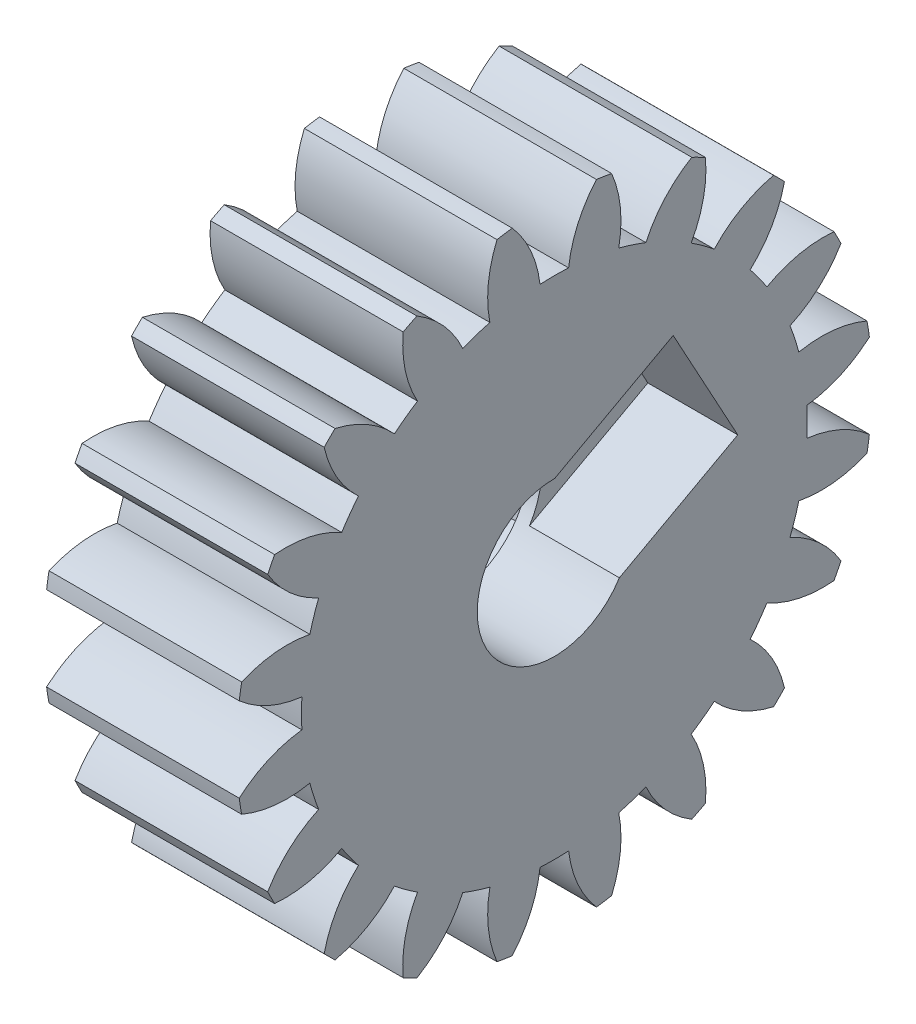
SolidWorks part; units mm, degrees
ref_plane "Plane1" through (0, 0, 0) normal (0, 0, 1) x (1, 0, 0)
ref_plane "Plane2" through (0, 0, 0) normal (0, 1, 0) x (1, 0, 0)
ref_plane "Plane3" through (0, 0, 0) normal (1, 0, 0) x (0, 0, -1)
sketch "HoldingSke" plane through (0, 0, 0) normal (0, 1, 0) x (1, 0, 0)
  line L0 (0, 0) -> (0.4176, -0.152)
  line L1 (-15, 0) -> (100, 0) construction
  line L2 (0, 0) -> (-2.1039, 2.3779)
  line L3 (0, 0) -> (-11.863, 4.5341)
  line L4 (0, 0) -> (8.1152, 2.9537)
  line L5 (0, 0) -> (-46.8476, -17.4728)
  line L6 (0, 0) -> (-8.2896, -5.593)
  line L7 (-2.1039, 2.3779) -> (8.6586, 51.2059)
  line L8 (-76.2, 54.61) -> (-76.1, 54.61)
  line L9 (-71.009, 38.7566) -> (-53.1078, 45.2721)
  line L10 (-76.2, 71.12) -> (104.1128, 71.12)
  line L11 (0, 0) -> (-10, 0)
  line L12 (-76.2, 101.6) -> (-76.123, 101.6)
  line L13 (24.9733, 27.94) -> (52.9518, 28.4284)
  line L14 (24.9733, 27.94) -> (24.9743, 27.94)
  line L15 (24.9733, 27.94) -> (100.4006, 29.5858)
  line L16 (-63.627, -2.25) -> (-12.827, -2.25)
  circle A0 centre (0, 0) radius 0.4
  circle A1 centre (0, 0) radius 19.6865
  circle A2 centre (0, 0) radius 37.5
  circle A3 centre (0, 0) radius 0.4
  dimension "MHD" = 39.373
  dimension "Hub_dia" = 75
  dimension "Bore" = 0.8
  dimension "MBD" = 0.8
  dimension "Num_teeth" = 20
  dimension "Pitch_radius" = 180.3128
  dimension "Pitch" = 0.4444
  dimension "Width" = 10
  dimension "Overall_len" = 50
  dimension "Show_teeth" = 20
  dimension "Thickness" = 10
  dimension "OAL" = 50.0001
  dimension "T_dim" = 0.1
  dimension "Ap" = 20
  dimension "H" = 19.05
  dimension "Backlash" = 0.077
  dimension "Addendum_fac" = 1
  dimension "Dedendum_fac" = 1.25
  dimension "Clearance_fac" = 0.25
  dimension "Dedendum_add" = 0.001
  dimension "Module" = 2.25
sketch "BasProSke" plane through (0, 0, 0) normal (0, 1, 0) x (1, 0, 0)
  line L0 (-10, 0) -> (60, 0) construction
  line L1 (0, 0) -> (0, 24.75)
  line L2 (0, 0) -> (15, 0)
  line L3 (15, 0) -> (15, 24.75)
  line L4 (15, 24.75) -> (0, 24.75)
  dimension "Diameter" = 49.5
  dimension "Thickness" = 15
revolve "Base-Revolve" add sketch "BasProSke" angle 360 about L0
sketch "TooCutSke" plane through (0, 0, 0) normal (1, 0, 0) x (0, 0, -1)
  line L1 (0, 0) -> (0, 107) construction
  line L2 (0, 0) -> (-1.9, 22.4196) construction
  line L3 (0, 0) -> (-7.021, 44.3291) construction
  line L4 (-1.9, 22.4196) -> (-3.5105, 22.1646) construction
  arc A0 (1.1119, 19.6551) -> (-1.1119, 19.6551) centre (0, 0) ccw
  arc A1 (3.3, 24.5546) -> (-3.3, 24.5546) centre (0, 0) ccw
  circle A2 centre (0, 0) radius 22.5 construction
  circle A3 centre (0, 0) radius 21.1431 construction
  arc A4 (-1.1119, 19.6551) -> (-3.3, 24.5546) centre (-10.0501, 18.6018) ccw
  arc A5 (3.3, 24.5546) -> (1.1119, 19.6551) centre (10.0501, 18.6018) ccw
  dimension "Root_dia" = 39.373
  dimension "Overcut_dia" = 49.5508
  dimension "Pitch_dia" = 45
  dimension "Base_dia" = 42.2862
  dimension "Flank_rad" = 9
  dimension "Half_ang" = 9
  dimension "Half_CT" = 1.6306
extrude "ToothCut" cut sketch "TooCutSke" along normal through all
fillet "Breaks" [suppressed] radius 0.045
fillet "RootFillets" [suppressed] radius 0.5635
pattern_circular "TeethCuts" count 20 over 360 about axis through (0, 0, 0) along (1, 0, 0) of "ToothCut", "RootFillets", "Breaks"
sketch "HubNeaOneSke" plane through (0, 0, 0) normal (-1, 0, 0) x (0, 0, 1)
  circle A0 centre (0, 0) radius 19.6865
  dimension "Diameter" = 39.373
extrude "HubNearOne" [suppressed] add sketch "HubNeaOneSke" along normal blind 35.0001
sketch "HubNeaBotSke" plane through (0, 0, 0) normal (-1, 0, 0) x (0, 0, 1)
  circle A0 centre (0, 0) radius 19.6865
  dimension "Diameter" = 39.373
extrude "HubNearBoth" [suppressed] add sketch "HubNeaBotSke" along normal blind 17.5
ref_plane "FarPln" through (15, 0, 0) normal (1, 0, 0) x (0, 0, -1)
sketch "HubFarSke" plane through (15, 0, 0) normal (1, 0, 0) x (0, 0, -1)
  circle A0 centre (0, 0) radius 19.6865
  dimension "Diameter" = 39.373
extrude "HubFar" [suppressed] add sketch "HubFarSke" along normal blind 17.5
sketch "BorSke" plane through (0, 0, 0) normal (1, 0, 0) x (0, 0, -1)
  circle A0 centre (0, 0) radius 6
  dimension "Diameter" = 12
extrude "Bore" cut sketch "BorSke" along normal mid plane 100.0001
sketch "KeySke" plane through (0, 0, 0) normal (1, 0, 0) x (0, 0, -1)
  line L0 (-0.05, 0) -> (-0.05, 0.5)
  line L1 (-0.05, 0.5) -> (0.05, 0.5)
  line L2 (0.05, 0.5) -> (0.05, 0)
  line L3 (0, 0) -> (0, 34) construction
  line L4 (-0.05, 0) -> (0.05, 0)
  dimension "Offset" = 0.5
  dimension "Width" = 0.1
extrude "Keyway" [suppressed] cut sketch "KeySke" along normal mid plane 100.0001
pattern_circular "Keyway2" [suppressed] count 2 every 90 about axis through (-10, 0, 0) along (1, 0, 0)
sketch "Sketch1" plane through (15, 0, 0) normal (1, 0, 0) x (0, 0, -1)
  line L0 (0.0359, 5.9999) -> (5.0641, -3.2178)
  line L1 (0.0359, 5.9999) -> (9.2536, 11.0282)
  line L2 (5.0641, -3.2178) -> (14.2819, 1.8104)
  line L3 (9.2536, 11.0282) -> (14.2819, 1.8104)
  circle A0 centre (0, 0) radius 6
  circle A1 centre (0, 0) radius 6 construction
  dimension "D1" = 0
  dimension "D4" = 12
  dimension "D2" = 6
  dimension "D3" = 6
  dimension "D5" = 10.5
  dimension "D6" = 10.5
extrude "Cut-Extrude1" cut sketch "Sketch1" against normal blind 7 contours L0 A0 | L0 A0 | A0 L0 L2 L3 L1
sketch "Sketch2" plane through (0, 0, 0) normal (-1, 0, 0) x (0, 0, 1)
  line L1 (13.038, -4.6914) -> (10.5819, 8.9455)
  line L2 (10.5819, 8.9455) -> (-2.4561, 13.637)
  line L3 (-2.4561, 13.637) -> (-13.038, 4.6914)
  line L4 (-13.038, 4.6914) -> (-10.5819, -8.9455)
  line L5 (-10.5819, -8.9455) -> (2.4561, -13.637)
  line L6 (2.4561, -13.637) -> (13.038, -4.6914)
  line L7 (4.6914, 13.038) -> (-8.9455, 10.5819)
  line L8 (-8.9455, 10.5819) -> (-13.637, -2.4561)
  line L9 (-13.637, -2.4561) -> (-4.6914, -13.038)
  line L10 (-4.6914, -13.038) -> (8.9455, -10.5819)
  line L11 (8.9455, -10.5819) -> (13.637, 2.4561)
  line L12 (13.637, 2.4561) -> (4.6914, 13.038)
  circle A0 centre (0, 0) radius 12 construction
  circle A1 centre (0, 0) radius 6 construction
  circle A2 centre (0, 0) radius 12 construction
  dimension "D1" = 0
  dimension "D2" = 24
  dimension "D3" = 24
  dimension "D5" = 0
  dimension "D4" = 30
extrude "Cut-Extrude2" cut sketch "Sketch2" against normal blind 7 contours L1 L12 L2 L7 L3 L8 L4 L9 L5 L10 L6 L11 | L8 L9 L4 | L9 L4 L5 | L9 L10 L5 | L10 L5 L6 | L10 L11 L6 | L11 L6 L1 | L12 L1 L2 | L11 L12 L1 | L2 L12 L7 | L7 L2 L3 | L7 L8 L3 | L8 L3 L4
equation "' \"Module@HoldingSke\" = 6.35"
equation "' \"Num_teeth@HoldingSke\" = 12"
equation "' \"Ap@HoldingSke\" =  20"
equation "' \"Width@HoldingSke\" = 0.5 * 25.4"
equation "' \"Hub_dia@HoldingSke\"= 1 * 25.4"
equation "' \"Overall_len@HoldingSke\" = 1.0 * 25.4"
equation "' \"Bore@HoldingSke\" = 0.75 * 25.4"
equation "' \"T_dim@HoldingSke\" = 0.1 * 25.4"
equation "' \"Width@KeySke\" = 0.25 * 25.4"
equation "' \"Show_teeth@HoldingSke\" = 13"
equation "' \"Backlash@HoldingSke\" = 0.009 * 25.4"
equation "' \"Addendum_fac@HoldingSke\" = 1.0"
equation "' \"Dedendum_fac@HoldingSke\" = 1.25"
equation "' \"Dedendum_add@HoldingSke\" = 0.00005 * 25.4"
equation "' \"Clearance_fac@HoldingSke\" = 0.25"
equation "\"Pitch@HoldingSke\" = 1 / \"Module@HoldingSke\""
equation "\"Overcut_dia@TooCutSke\" = (\"Num_teeth@HoldingSke\" + 2 * \"Addendum_fac@HoldingSke\") / \"Pitch@HoldingSke\" + 0.002 * 25.4"
equation "\"Pitch_dia@TooCutSke\" = \"Num_teeth@HoldingSke\" / \"Pitch@HoldingSke\""
equation "\"Base_dia@TooCutSke\" = \"Num_teeth@HoldingSke\" / \"Pitch@HoldingSke\" * cos((\"Ap@HoldingSke\"  * 3.14159265 / 180))"
equation "\"Root_dia@TooCutSke\" = (\"Num_teeth@HoldingSke\" + 2) / \"Pitch@HoldingSke\" - 2 * (\"Addendum_fac@HoldingSke\" + \"Dedendum_fac@HoldingSke\") / \"Pitch@HoldingSke\" - \"Dedendum_add@HoldingSke\" * 2"
equation "\"Half_ang@TooCutSke\" = 180 / \"Num_teeth@HoldingSke\""
equation "\"Half_CT@TooCutSke\" = \"Num_teeth@HoldingSke\" / \"Pitch@HoldingSke\" * sin((3.14159265 / 2 / \"Num_teeth@HoldingSke\")) / 2 - 7 * \"Backlash@HoldingSke\" / 4"
equation "\"Flank_rad@TooCutSke\" = \"Num_teeth@HoldingSke\" / \"Pitch@HoldingSke\" / 5"
equation "\"Radius@RootFillets\" = \"Clearance_fac@HoldingSke\" / \"Pitch@HoldingSke\" + \"Dedendum_add@HoldingSke\""
equation "\"Break_rad@Breaks\" = 0.02 / \"Pitch@HoldingSke\""
equation "\"Thickness@HoldingSke\" = \"Width@HoldingSke\""
equation "\"OAL@HoldingSke\" = \"Thickness@HoldingSke\""
equation "\"MHD@HoldingSke\" = (\"Num_teeth@HoldingSke\" + 2) / \"Pitch@HoldingSke\" - 2 * (\"Addendum_fac@HoldingSke\" + \"Dedendum_fac@HoldingSke\")  / \"Pitch@HoldingSke\" - \"Dedendum_add@HoldingSke\" * 2"
equation "\"MBD@HoldingSke\" = (\"Num_teeth@HoldingSke\" + 2) / \"Pitch@HoldingSke\" - 2 * (\"Addendum_fac@HoldingSke\" + \"Dedendum_fac@HoldingSke\")  / \"Pitch@HoldingSke\" - \"Dedendum_add@HoldingSke\" * 2 - 0.002 * 25.4"
equation "\"MHD@HoldingSke\" = ((sgn( \"MHD@HoldingSke\" - \"Hub_dia@HoldingSke\" )-1)*( \"MHD@HoldingSke\" - \"Hub_dia@HoldingSke\" ))/-2+ \"Hub_dia@HoldingSke\""
equation "\"MBD@HoldingSke\" = ((sgn( \"MBD@HoldingSke\" - \"Bore@HoldingSke\" )-1)*( \"MBD@HoldingSke\" - \"Bore@HoldingSke\" ))/-2+ \"Bore@HoldingSke\""
equation "\"OAL@HoldingSke\" = ((sgn( \"OAL@HoldingSke\" - \"Overall_len@HoldingSke\" )+1)*( \"OAL@HoldingSke\" - \"Overall_len@HoldingSke\" ))/2 + \"Overall_len@HoldingSke\" + 0.000002 * 25.4"
equation "\"Num_teeth@TeethCuts\" = int( \"Show_teeth@HoldingSke\" ) + 1"
equation "\"Num_teeth@TeethCuts\" = ((sgn( \"Num_teeth@TeethCuts\" - \"Num_teeth@HoldingSke\" )-1)*( \"Num_teeth@TeethCuts\" - \"Num_teeth@HoldingSke\" ))/-2+ \"Num_teeth@HoldingSke\""
equation "\"Num_teeth@TeethCuts\" = ((sgn( \"Num_teeth@TeethCuts\" - 2.0)+1)*( \"Num_teeth@TeethCuts\" - 2.0))/2 +2.0"
equation "\"Angle@TeethCuts\" = 360.0 / \"Num_teeth@HoldingSke\""
equation "\"Diameter@BasProSke\" = (\"Num_teeth@HoldingSke\" + 2 * \"Addendum_fac@HoldingSke\") / \"Pitch@HoldingSke\""
equation "\"Thickness@BasProSke\"=15mm"
equation "' \"Fillet_rad@BasProSke\" =  \"Thickness@HoldingSke\" * 0.05"
equation "\"MHD@HoldingSke\" = ((sgn( \"MHD@HoldingSke\" - \"Root_dia@TooCutSke\" )-1)*( \"MHD@HoldingSke\" - \"Root_dia@TooCutSke\" ))/-2+ \"Root_dia@TooCutSke\""
equation "\"Diameter@HubNeaOneSke\" = \"MHD@HoldingSke\""
equation "\"Length@HubNearOne\" = \"OAL@HoldingSke\" - \"Thickness@BasProSke\""
equation "\"Diameter@HubNeaBotSke\" = \"MHD@HoldingSke\""
equation "\"Length@HubNearBoth\" = ( \"OAL@HoldingSke\" - \"Thickness@BasProSke\" ) / 2.0"
equation "\"Thickness@FarPln\"=15"
equation "\"Diameter@HubFarSke\" = \"MHD@HoldingSke\""
equation "\"Length@HubFar\" = ( \"OAL@HoldingSke\" - \"Thickness@BasProSke\" ) / 2.0"
equation "\"Diameter@BorSke\"=12mm"
equation "\"D1@Bore\" = \"OAL@HoldingSke\" * 2.0"
equation "\"D1@Keyway\" = \"OAL@HoldingSke\" * 2.0"
equation "\"Offset@KeySke\" = \"T_dim@HoldingSke\" + \"MBD@HoldingSke\" / 2.0"
